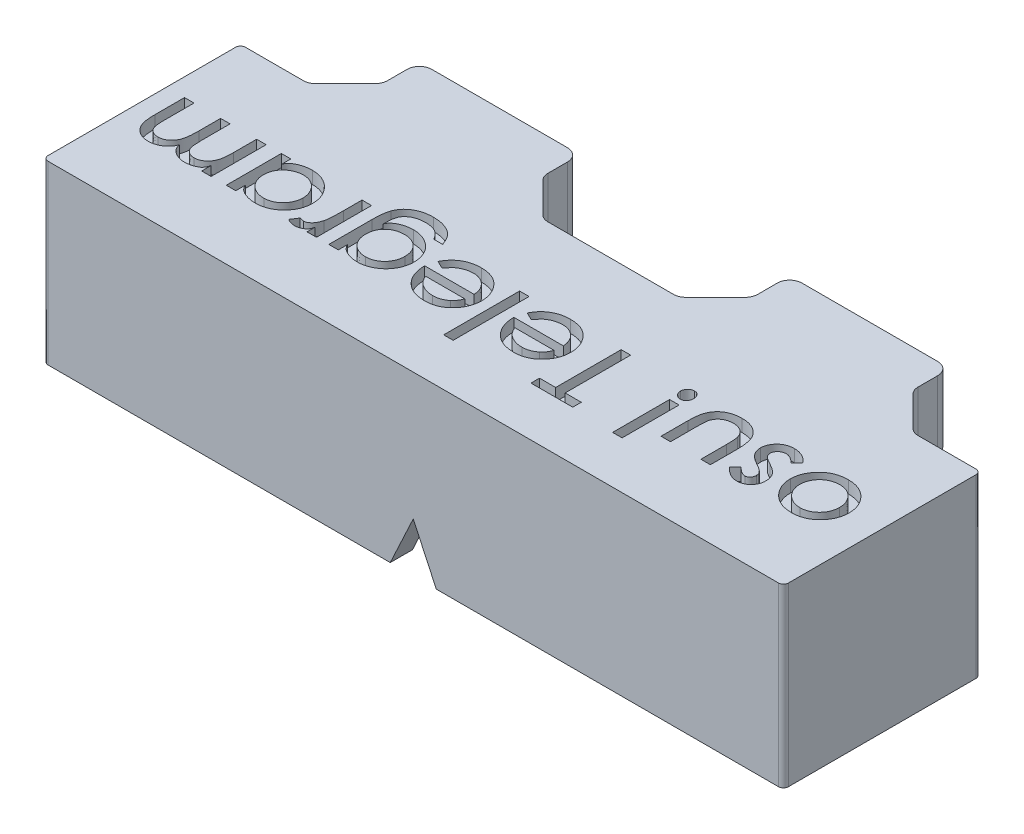
SolidWorks part; units mm, degrees
ref_plane "Front Plane" through (0, 0, 0) normal (0, 0, 1) x (1, 0, 0)
ref_plane "Top Plane" through (0, 0, 0) normal (0, 1, 0) x (1, 0, 0)
ref_plane "Right Plane" through (0, 0, 0) normal (1, 0, 0) x (0, 0, -1)
sketch "Sketch1" plane through (0, 0, 0) normal (0, 1, 0) x (1, 0, 0)
  line L0 (0, 0) -> (60, 0)
  line L1 (60, 0) -> (60, -16)
  line L2 (60, -16) -> (0, -16)
  line L3 (0, -16) -> (0, 0)
  dimension "D1" = 60
  dimension "D2" = 16
extrude "Boss-Extrude1" add sketch "Sketch1" against normal blind 6.5
ref_plane "Plane1" through (15, 0, 0) normal (-1, 0, 0) x (0, 0, 1)
ref_plane "Plane2" through (45, 0, 0) normal (1, 0, 0) x (0, 0, -1)
sketch "Sketch2" plane through (15, 0, 0) normal (-1, 0, 0) x (0, 0, 1)
  line L0 (0, -6.5) -> (16, -6.5) construction
  line L1 (12.05, -6.5) -> (3.95, -6.5)
  arc A0 (3.95, -6.5) -> (12.05, -6.5) centre (8, -6.5) cw
  point P7 (8, -6.5)
  dimension "D1" = 8.1
extrude "Cut-Extrude1" cut sketch "Sketch2" against normal blind 10.1 and the other way blind 10.1
sketch "Sketch3" plane through (45, 0, 0) normal (1, 0, 0) x (0, 0, -1)
  line L0 (-12.05, -6.5) -> (-3.95, -6.5) construction
  line L1 (-12.05, -6.5) -> (-3.95, -6.5)
  arc A0 (-3.95, -6.5) -> (-12.05, -6.5) centre (-8, -6.5) ccw construction
  arc A1 (-3.95, -6.5) -> (-12.05, -6.5) centre (-8, -6.5) ccw
extrude "Cut-Extrude5" cut sketch "Sketch3" against normal blind 10.1 and the other way blind 10.1
sketch "Sketch4" plane through (0, -6.5, 0) normal (0, -1, 0) x (1, 0, 0)
  line L0 (1.8, 0) -> (1.8, 14.2)
  line L1 (60, 0) -> (0, 0) construction
  line L2 (1.8, 14.2) -> (58.2, 14.2)
  line L3 (58.2, 14.2) -> (58.2, 0)
  line L4 (58.2, 0) -> (60, 0)
  line L5 (60, 0) -> (60, 16)
  line L6 (60, 16) -> (0, 16)
  line L7 (0, 16) -> (0, 0)
  line L8 (0, 0) -> (1.8, 0)
  dimension "D1" = 1.8
  dimension "D2" = 1.8
extrude "Boss-Extrude2" add sketch "Sketch4" along normal blind 7.8
sketch "Sketch5" plane through (0, 0, 0) normal (0, 0, -1) x (-1, 0, 0)
  line L0 (-51.5, -6.5) -> (-51.5, -5.5)
  line L1 (-58.2, -6.5) -> (-1.8, -6.5) construction
  line L2 (-51.5, -5.5) -> (-38.5, -5.5)
  line L3 (-38.5, -5.5) -> (-38.5, -6.5)
  line L4 (-1.8, -6.5) -> (-58.2, -6.5) construction
  line L5 (-38.5, -6.5) -> (-51.5, -6.5)
  line L6 (-21.5, -6.5) -> (-21.5, -5.5)
  line L7 (-21.5, -5.5) -> (-8.5, -5.5)
  line L8 (-8.5, -5.5) -> (-8.5, -6.5)
  line L9 (-8.5, -6.5) -> (-21.5, -6.5)
  line L10 (-55.1, -6.5) -> (-34.9, -6.5) construction
  line L12 (-4.9, -6.5) -> (-25.1, -6.5) construction
  point P14 (-45, -6.5)
  point P15 (-45, -6.5)
  point P18 (-15, -6.5)
  point P19 (-15, -6.5)
  dimension "D1" = 1
  dimension "D2" = 13
extrude "Cut-Extrude6" cut sketch "Sketch5" against normal blind 8
sketch "Sketch6" plane through (0, 0, 0) normal (0, 0, -1) x (-1, 0, 0)
  line L0 (-51.5, -5.5) -> (-38.5, -5.5)
  line L1 (-38.5, -5.5) -> (-38.5, 0)
  line L2 (-60, 0) -> (0, 0) construction
  line L3 (-38.5, 0) -> (-51.5, 0)
  line L4 (-51.5, 0) -> (-51.5, -5.5)
  line L5 (-21.5, -5.5) -> (-8.5, -5.5)
  line L6 (-8.5, -5.5) -> (-8.5, 0)
  line L7 (-8.5, 0) -> (-21.5, 0)
  line L8 (-21.5, 0) -> (-21.5, -5.5)
extrude "Boss-Extrude3" add sketch "Sketch6" along normal blind 6
chamfer "Chamfer1" distance 3 angle 45 4 edges at (21.5, -2.75, 0) (8.5, -2.75, 0) (51.5, -2.75, 0) (38.5, -2.75, 0)
fillet "Fillet2" radius 1 12 edges at (21.5, -2.75, -6) (8.5, -2.75, -6) (8.5, -2.75, -3) (5.5, -2.75, 0) (21.5, -2.75, -3) (35.5, -2.75, 0) (24.5, -2.75, 0) (51.5, -2.75, -3) (54.5, -2.75, 0) (38.5, -2.75, -3) (51.5, -2.75, -6) (38.5, -2.75, -6)
fillet "Fillet3" radius 0.4 12 edges at (1.8, -10.4, 0) (1.8, -10.4, 14.2) (58.2, -10.4, 14.2) (58.2, -10.4, 0) (38.5, -6, 0) (51.5, -6, 0) (8.5, -6, 0) (21.5, -6, 0) (0, -7.15, 0) (60, -7.15, 0) (60, -7.15, 16) (0, -7.15, 16)
sketch "Sketch7" plane through (0, 0, 0) normal (0, 1, 0) x (1, 0, 0)
  line L0 (60, -6) -> (0, -6) construction
  line L1 (0.4, -16) -> (59.6, -16) construction
  text T0 "<b>osu! Telegram</b>" font "Century Gothic" height 6
  point P7 (30, -16)
  point P8 (30, -6)
  dimension "D1" = 60
  dimension "D2" = 10
extrude "Cut-Extrude7" cut sketch "Sketch7" against normal blind 1
sketch "Sketch8" plane through (0, 0, 16) normal (0, 0, 1) x (1, 0, 0)
  line L0 (28.1348, -14.3) -> (30, -10.3)
  line L1 (59.6, -14.3) -> (0.4, -14.3) construction
  line L2 (30, -10.3) -> (31.8652, -14.3)
  line L3 (31.8652, -14.3) -> (28.1348, -14.3)
  point P4 (30, -14.3)
  point P6 (30, -14.3)
  dimension "D1" = 4
  dimension "D2" = 50
extrude "Cut-Extrude8" cut sketch "Sketch8" against normal up to next
